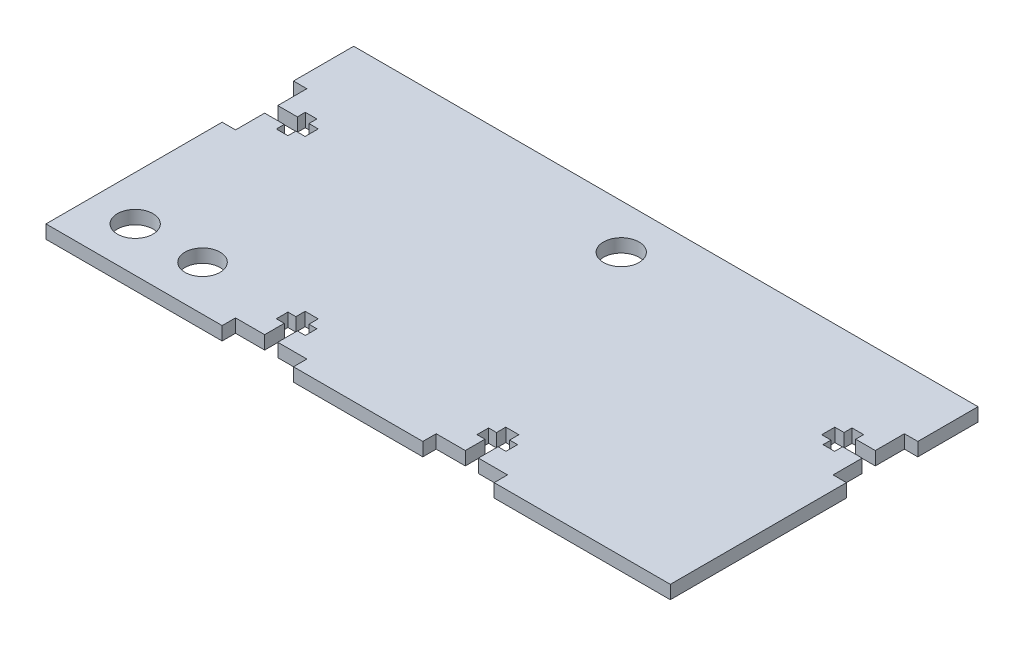
SolidWorks part; units mm, degrees
ref_plane "Front Plane" through (0, 0, 0) normal (0, 0, 1) x (1, 0, 0)
ref_plane "Top Plane" through (0, 0, 0) normal (0, 1, 0) x (1, 0, 0)
ref_plane "Right Plane" through (0, 0, 0) normal (1, 0, 0) x (0, 0, -1)
sketch "Sketch1" plane through (0, 0, 0) normal (0, 1, 0) x (1, 0, 0)
  line L1 (-70, -70) -> (70, -70)
  line L2 (-70, -70) -> (-70, 70)
  line L3 (-70, 70) -> (70, 70)
  line L4 (70, -70) -> (70, 70)
  line L5 (-70, -70) -> (70, 70) construction
  line L6 (-70, 70) -> (70, -70) construction
  point P0 (0, 0)
  dimension "D1" = 140
extrude "Boss-Extrude1" add sketch "Sketch1" along normal blind 3
sketch "Sketch2" plane through (0, 3, 0) normal (0, 1, 0) x (1, 0, 0)
  line L0 (-30.5, 70) -> (-30.5, 67)
  line L1 (70, 70) -> (-70, 70) construction
  line L2 (-30.5, 67) -> (-14.5, 67)
  line L3 (-14.5, 67) -> (-14.5, 70)
  line L4 (-14.5, 70) -> (-30.5, 70)
  line L5 (-70, 70) -> (-70, -70) construction
  line L6 (-1.65, 0) -> (1.65, 0) construction
  line L7 (-14.5, -67) -> (-14.5, -70)
  line L8 (-30.5, -67) -> (-14.5, -67)
  line L9 (-30.5, -70) -> (-30.5, -67)
  line L10 (-14.5, -70) -> (-30.5, -70)
  line L11 (0, -1.65) -> (0, 1.65) construction
  line L12 (30.5, -67) -> (14.5, -67)
  line L13 (30.5, -70) -> (30.5, -67)
  line L14 (14.5, -70) -> (30.5, -70)
  line L15 (14.5, -67) -> (14.5, -70)
  line L16 (14.5, 67) -> (14.5, 70)
  line L17 (30.5, 67) -> (14.5, 67)
  line L18 (30.5, 70) -> (30.5, 67)
  line L19 (14.5, 70) -> (30.5, 70)
  line L20 (-70, 30.5) -> (-67, 30.5)
  line L21 (-67, 30.5) -> (-67, 14.5)
  line L22 (-67, 14.5) -> (-70, 14.5)
  line L23 (-70, 14.5) -> (-70, 30.5)
  line L24 (-67, -14.5) -> (-70, -14.5)
  line L25 (-67, -30.5) -> (-67, -14.5)
  line L26 (-70, -30.5) -> (-67, -30.5)
  line L27 (-70, -14.5) -> (-70, -30.5)
  line L28 (67, -30.5) -> (67, -14.5)
  line L29 (70, -30.5) -> (67, -30.5)
  line L30 (70, -14.5) -> (70, -30.5)
  line L31 (67, -14.5) -> (70, -14.5)
  line L32 (67, 14.5) -> (70, 14.5)
  line L33 (67, 30.5) -> (67, 14.5)
  line L34 (70, 30.5) -> (67, 30.5)
  line L35 (70, 14.5) -> (70, 30.5)
  dimension "D1" = 16
  dimension "D2" = 3
  dimension "D3" = 39.5
  dimension "D4" = 16
  dimension "D5" = 3
  dimension "39.50" = 39.5
extrude "Cut-Extrude1" cut sketch "Sketch2" against normal blind 3 contours L4 L0 L2 L3 | L16 L19 L18 L17 | L23 L20 L21 L22 | L24 L27 L26 L25 | L7 L10 L9 L8 | L12 L15 L14 L13 | L28 L31 L30 L29 | L32 L35 L34 L33
sketch "Sketch3" plane through (0, 3, 0) normal (0, 1, 0) x (1, 0, 0)
  line L0 (-67, 70) -> (-67, 60)
  line L1 (-30.5, 70) -> (-70, 70) construction
  line L2 (-67, 60) -> (-70, 60)
  line L3 (-70, 70) -> (-70, 30.5) construction
  line L4 (-70, 60) -> (-70, 70)
  line L5 (-70, 70) -> (-67, 70)
  dimension "D1" = 3
  dimension "D2" = 10
extrude "Cut-Extrude2" cut sketch "Sketch3" against normal blind 10
sketch "Sketch4" plane through (0, 3, 0) normal (0, 1, 0) x (1, 0, 0)
  line L0 (70, 70) -> (67, 70)
  line L1 (70, 70) -> (30.5, 70) construction
  line L2 (67, 70) -> (67, 60)
  line L3 (67, 60) -> (70, 60)
  line L4 (70, 30.5) -> (70, 70) construction
  line L5 (70, 60) -> (70, 70)
  dimension "D1" = 3
  dimension "D2" = 10
extrude "Cut-Extrude3" cut sketch "Sketch4" against normal blind 3 contours L5 L0 L2 L3
sketch "Sketch5" plane through (0, 3, 0) normal (0, 1, 0) x (1, 0, 0)
  line L0 (-22.5, 67) -> (-22.5, -67) construction
  line L1 (-30.5, 67) -> (-14.5, 67) construction
  line L2 (-30.5, -67) -> (-14.5, -67) construction
  line L3 (-21.03, 67) -> (-23.97, 67)
  line L4 (-23.97, 67) -> (-23.97, 62.6)
  line L5 (-23.97, 62.6) -> (-25.75, 62.6)
  line L6 (-25.75, 62.6) -> (-25.75, 60)
  line L7 (-25.75, 60) -> (-23.97, 60)
  line L8 (-23.97, 60) -> (-23.97, 57.92)
  line L9 (-23.97, 57.92) -> (-21.03, 57.92)
  line L10 (-21.03, 67) -> (-21.03, 62.6)
  line L11 (-21.03, 62.6) -> (-19.25, 62.6)
  line L12 (-19.25, 62.6) -> (-19.25, 60)
  line L13 (-19.25, 60) -> (-21.03, 60)
  line L14 (-21.03, 60) -> (-21.03, 57.92)
  line L15 (-1.65, 0) -> (1.65, 0) construction
  line L16 (-21.03, -67) -> (-21.03, -62.6)
  line L17 (-21.03, -62.6) -> (-19.25, -62.6)
  line L18 (-19.25, -62.6) -> (-19.25, -60)
  line L19 (-19.25, -60) -> (-21.03, -60)
  line L20 (-21.03, -60) -> (-21.03, -57.92)
  line L21 (-23.97, -57.92) -> (-21.03, -57.92)
  line L22 (-23.97, -60) -> (-23.97, -57.92)
  line L23 (-25.75, -60) -> (-23.97, -60)
  line L24 (-25.75, -62.6) -> (-25.75, -60)
  line L25 (-23.97, -62.6) -> (-25.75, -62.6)
  line L26 (-23.97, -67) -> (-23.97, -62.6)
  line L27 (-21.03, -67) -> (-23.97, -67)
  line L28 (0, -1.65) -> (0, 1.65) construction
  line L29 (21.03, 67) -> (21.03, 62.6)
  line L30 (21.03, 62.6) -> (19.25, 62.6)
  line L31 (19.25, 62.6) -> (19.25, 60)
  line L32 (19.25, 60) -> (21.03, 60)
  line L33 (21.03, 60) -> (21.03, 57.92)
  line L34 (23.97, 57.92) -> (21.03, 57.92)
  line L35 (23.97, 60) -> (23.97, 57.92)
  line L36 (25.75, 60) -> (23.97, 60)
  line L37 (25.75, 62.6) -> (25.75, 60)
  line L38 (23.97, 62.6) -> (25.75, 62.6)
  line L39 (23.97, 67) -> (23.97, 62.6)
  line L40 (21.03, 67) -> (23.97, 67)
  line L41 (21.03, -67) -> (23.97, -67)
  line L42 (23.97, -67) -> (23.97, -62.6)
  line L43 (23.97, -62.6) -> (25.75, -62.6)
  line L44 (25.75, -62.6) -> (25.75, -60)
  line L45 (25.75, -60) -> (23.97, -60)
  line L46 (23.97, -60) -> (23.97, -57.92)
  line L47 (23.97, -57.92) -> (21.03, -57.92)
  line L48 (21.03, -60) -> (21.03, -57.92)
  line L49 (19.25, -60) -> (21.03, -60)
  line L50 (19.25, -62.6) -> (19.25, -60)
  line L51 (21.03, -62.6) -> (19.25, -62.6)
  line L52 (21.03, -67) -> (21.03, -62.6)
  point P20 (-22.5, 57.92)
  dimension "D1" = 2.94
  dimension "D2" = 2.08
  dimension "D3" = 2.6
  dimension "D4" = 4.4
  dimension "D5" = 1.78
extrude "Cut-Extrude4" cut sketch "Sketch5" against normal blind 3
sketch "Sketch6" plane through (0, 3, 0) normal (0, 1, 0) x (1, 0, 0)
  line L0 (67, -22.5) -> (-67, -22.5) construction
  line L1 (67, -30.5) -> (67, -14.5) construction
  line L2 (-67, -30.5) -> (-67, -14.5) construction
  line L3 (67, -21.03) -> (67, -23.97)
  line L4 (67, -23.97) -> (62.6, -23.97)
  line L5 (62.6, -23.97) -> (62.6, -25.75)
  line L6 (62.6, -25.75) -> (60, -25.75)
  line L7 (60, -25.75) -> (60, -23.97)
  line L8 (60, -23.97) -> (57.92, -23.97)
  line L9 (57.92, -23.97) -> (57.92, -21.03)
  line L10 (67, -21.03) -> (62.6, -21.03)
  line L11 (62.6, -21.03) -> (62.6, -19.25)
  line L12 (62.6, -19.25) -> (60, -19.25)
  line L13 (60, -19.25) -> (60, -21.03)
  line L14 (60, -21.03) -> (57.92, -21.03)
  line L15 (-1.65, 0) -> (1.65, 0) construction
  line L16 (67, 21.03) -> (62.6, 21.03)
  line L17 (62.6, 21.03) -> (62.6, 19.25)
  line L18 (62.6, 19.25) -> (60, 19.25)
  line L19 (60, 19.25) -> (60, 21.03)
  line L20 (60, 21.03) -> (57.92, 21.03)
  line L21 (57.92, 23.97) -> (57.92, 21.03)
  line L22 (60, 23.97) -> (57.92, 23.97)
  line L23 (60, 25.75) -> (60, 23.97)
  line L24 (62.6, 25.75) -> (60, 25.75)
  line L25 (62.6, 23.97) -> (62.6, 25.75)
  line L26 (67, 23.97) -> (62.6, 23.97)
  line L27 (67, 21.03) -> (67, 23.97)
  line L28 (0, -1.65) -> (0, 1.65) construction
  line L29 (-67, -21.03) -> (-62.6, -21.03)
  line L30 (-62.6, -21.03) -> (-62.6, -19.25)
  line L31 (-62.6, -19.25) -> (-60, -19.25)
  line L32 (-60, -19.25) -> (-60, -21.03)
  line L33 (-60, -21.03) -> (-57.92, -21.03)
  line L34 (-57.92, -23.97) -> (-57.92, -21.03)
  line L35 (-60, -23.97) -> (-57.92, -23.97)
  line L36 (-60, -25.75) -> (-60, -23.97)
  line L37 (-62.6, -25.75) -> (-60, -25.75)
  line L38 (-62.6, -23.97) -> (-62.6, -25.75)
  line L39 (-67, -23.97) -> (-62.6, -23.97)
  line L40 (-67, -21.03) -> (-67, -23.97)
  line L41 (-67, 21.03) -> (-67, 23.97)
  line L42 (-67, 23.97) -> (-62.6, 23.97)
  line L43 (-62.6, 23.97) -> (-62.6, 25.75)
  line L44 (-62.6, 25.75) -> (-60, 25.75)
  line L45 (-60, 25.75) -> (-60, 23.97)
  line L46 (-60, 23.97) -> (-57.92, 23.97)
  line L47 (-57.92, 23.97) -> (-57.92, 21.03)
  line L48 (-60, 21.03) -> (-57.92, 21.03)
  line L49 (-60, 19.25) -> (-60, 21.03)
  line L50 (-62.6, 19.25) -> (-60, 19.25)
  line L51 (-62.6, 21.03) -> (-62.6, 19.25)
  line L52 (-67, 21.03) -> (-62.6, 21.03)
  point P20 (57.92, -22.5)
  dimension "D1" = 2.94
  dimension "D2" = 1.78
  dimension "D3" = 2.6
  dimension "D4" = 2.08
  dimension "D5" = 4.4
extrude "Cut-Extrude5" cut sketch "Sketch6" against normal blind 3
sketch "Sketch8" plane through (0, 3, 0) normal (0, 1, 0) x (1, 0, 0)
  line L0 (-70, 30.5) -> (-67, 30.5)
  line L1 (-67, 30.5) -> (-67, 23.97)
  line L2 (-67, 23.97) -> (-62.6, 23.97)
  line L3 (-62.6, 23.97) -> (-62.6, 25.75)
  line L4 (-62.6, 25.75) -> (-60, 25.75)
  line L5 (-60, 25.75) -> (-60, 23.97)
  line L6 (-60, 23.97) -> (-57.92, 23.97)
  line L7 (-57.92, 23.97) -> (-57.92, 21.03)
  line L8 (-57.92, 21.03) -> (-60, 21.03)
  line L9 (-60, 21.03) -> (-60, 19.25)
  line L10 (-60, 19.25) -> (-62.6, 19.25)
  line L11 (-62.6, 19.25) -> (-62.6, 21.03)
  line L12 (-62.6, 21.03) -> (-67, 21.03)
  line L13 (-67, 21.03) -> (-67, 14.5)
  line L14 (-67, 14.5) -> (-70, 14.5)
  line L15 (-70, 14.5) -> (-70, 30.5)
extrude "Boss-Extrude4" add sketch "Sketch8" against normal blind 3
sketch "Sketch10" plane through (0, 3, 0) normal (0, 1, 0) x (1, 0, 0)
  line L0 (70, 30.5) -> (67, 30.5)
  line L1 (67, 30.5) -> (67, 23.97)
  line L2 (67, 23.97) -> (62.6, 23.97)
  line L3 (62.6, 23.97) -> (62.6, 25.75)
  line L4 (62.6, 25.75) -> (60, 25.75)
  line L5 (60, 25.75) -> (60, 23.97)
  line L6 (60, 23.97) -> (57.92, 23.97)
  line L7 (57.92, 23.97) -> (57.92, 21.03)
  line L8 (57.92, 21.03) -> (60, 21.03)
  line L9 (60, 21.03) -> (60, 19.25)
  line L10 (60, 19.25) -> (62.6, 19.25)
  line L11 (62.6, 19.25) -> (62.6, 21.03)
  line L12 (62.6, 21.03) -> (67, 21.03)
  line L13 (67, 21.03) -> (67, 14.5)
  line L14 (67, 14.5) -> (70, 14.5)
  line L15 (70, 14.5) -> (70, 30.5)
extrude "Boss-Extrude5" add sketch "Sketch10" against normal blind 3
sketch "Sketch12" plane through (0, 3, 0) normal (0, 1, 0) x (1, 0, 0)
  line L0 (-67, 70) -> (-70, 70)
  line L1 (-70, 70) -> (-70, 67)
  line L2 (-70, 67) -> (-67, 67)
  line L3 (-67, 60) -> (-67, 70) construction
  line L4 (-67, 67) -> (-67, 70)
  dimension "D1" = 3
  dimension "D2" = 3
extrude "Boss-Extrude6" add sketch "Sketch12" against normal blind 3
sketch "Sketch13" plane through (0, 3, 0) normal (0, 1, 0) x (1, 0, 0)
  line L0 (67, 70) -> (70, 70)
  line L1 (70, 70) -> (70, 67)
  line L2 (70, 67) -> (67, 67)
  line L3 (67, 70) -> (67, 60) construction
  line L4 (67, 67) -> (67, 70)
  dimension "D1" = 3
  dimension "D2" = 3
extrude "Boss-Extrude7" add sketch "Sketch13" against normal blind 3
sketch "Sketch14" plane through (0, 3, 0) normal (0, 1, 0) x (1, 0, 0)
  line L0 (-30.5, 70) -> (-14.5, 70)
  line L1 (-14.5, 70) -> (-14.5, 67)
  line L2 (-14.5, 67) -> (-21.03, 67)
  line L3 (-21.03, 67) -> (-21.03, 62.6)
  line L4 (-21.03, 62.6) -> (-19.25, 62.6)
  line L5 (-19.25, 62.6) -> (-19.25, 60)
  line L6 (-19.25, 60) -> (-21.03, 60)
  line L7 (-21.03, 60) -> (-21.03, 57.92)
  line L8 (-21.03, 57.92) -> (-23.97, 57.92)
  line L9 (-23.97, 57.92) -> (-23.97, 60)
  line L10 (-23.97, 60) -> (-25.75, 60)
  line L11 (-25.75, 60) -> (-25.75, 62.6)
  line L12 (-25.75, 62.6) -> (-23.97, 62.6)
  line L13 (-23.97, 62.6) -> (-23.97, 67)
  line L14 (-23.97, 67) -> (-30.5, 67)
  line L15 (-30.5, 67) -> (-30.5, 70)
  line L16 (14.5, 70) -> (30.5, 70)
  line L17 (30.5, 70) -> (30.5, 67)
  line L18 (30.5, 67) -> (23.97, 67)
  line L19 (23.97, 67) -> (23.97, 62.6)
  line L20 (23.97, 62.6) -> (25.75, 62.6)
  line L21 (25.75, 62.6) -> (25.75, 60)
  line L22 (25.75, 60) -> (23.97, 60)
  line L23 (23.97, 60) -> (23.97, 57.92)
  line L24 (23.97, 57.92) -> (21.03, 57.92)
  line L25 (21.03, 57.92) -> (21.03, 60)
  line L26 (21.03, 60) -> (19.25, 60)
  line L27 (19.25, 60) -> (19.25, 62.6)
  line L28 (19.25, 62.6) -> (21.03, 62.6)
  line L29 (21.03, 62.6) -> (21.03, 67)
  line L30 (21.03, 67) -> (14.5, 67)
  line L31 (14.5, 67) -> (14.5, 70)
extrude "Boss-Extrude8" add sketch "Sketch14" against normal blind 3
sketch "Sketch15" plane through (0, 3, 0) normal (0, 1, 0) x (1, 0, 0)
  line L0 (-70, 0) -> (70, 0)
  line L1 (-70, 60) -> (-70, -14.5) construction
  line L2 (70, -14.5) -> (70, 60) construction
  line L3 (-70, -1) -> (70, -1)
  line L4 (-70, 0) -> (-70, -1)
  line L5 (70, 0) -> (70, -1)
  dimension "D1" = 1
extrude "Cut-Extrude6" cut sketch "Sketch15" against normal blind 3
sketch "Sketch16" plane through (0, 3, 0) normal (0, 1, 0) x (1, 0, 0)
  line L1 (-70, 70) -> (70, 70)
  line L2 (-70, 70) -> (-70, 0)
  line L3 (-70, 0) -> (70, 0)
  line L4 (70, 70) -> (70, 0)
extrude "Cut-Extrude8" cut sketch "Sketch16" against normal blind 3
sketch "Sketch17" plane through (0, 3, 0) normal (0, 1, 0) x (1, 0, 0)
  line L0 (0, -70) -> (0, -1) construction
  line L5 (-14.5, -70) -> (14.5, -70) construction
  line L6 (-70, -1) -> (70, -1) construction
  line L8 (-70, -30.5) -> (-70, -70) construction
  line L9 (-70, -70) -> (-30.5, -70) construction
  circle A0 centre (0, -11) radius 3.99
  circle A1 centre (-60, -60) radius 3.99
  dimension "D1" = 7.98
  dimension "D3" = 7.98
  dimension "D2" = 10
  dimension "D4" = 10
  dimension "D5" = 10
extrude "Cut-Extrude11" cut sketch "Sketch17" against normal blind 3
sketch "Sketch18" plane through (0, 3, 0) normal (0, 1, 0) x (1, 0, 0)
  line L0 (-70, -70) -> (-30.5, -70) construction
  line L1 (-70, -30.5) -> (-70, -70) construction
  circle A0 centre (-45, -59.9) radius 3.935
  dimension "D1" = 7.87
  dimension "D2" = 10.1
  dimension "D3" = 25
extrude "Cut-Extrude12" cut sketch "Sketch18" against normal blind 3
